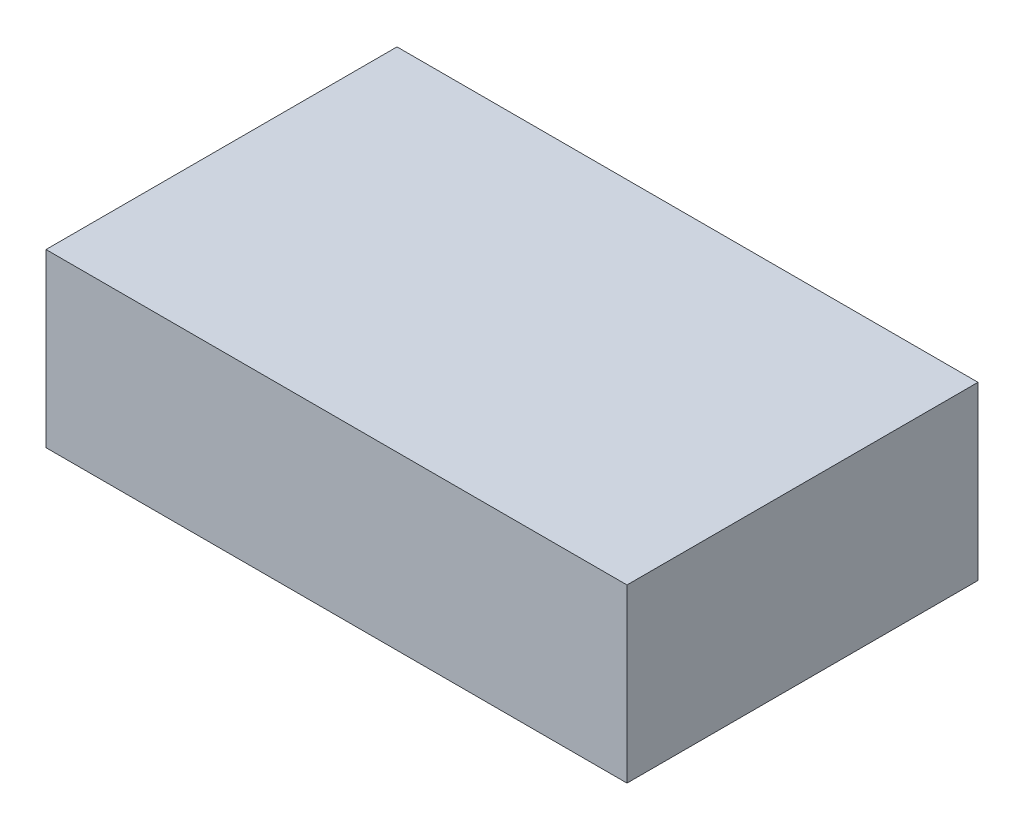
SolidWorks part; units mm, degrees
material "Brass"
ref_plane "Front Plane" through (0, 0, 0) normal (0, 0, 1) x (1, 0, 0)
ref_plane "Top Plane" through (0, 0, 0) normal (0, 1, 0) x (1, 0, 0)
ref_plane "Right Plane" through (0, 0, 0) normal (1, 0, 0) x (0, 0, -1)
sketch "Sketch1" plane through (0, 0, 0) normal (0, 1, 0) x (1, 0, 0)
  line L0 (1.38, -1.38) -> (3.92, -1.38) construction
  line L1 (0, 0) -> (18, 0)
  line L2 (0, 0) -> (0, -13)
  line L3 (0, -13) -> (18, -13)
  line L4 (18, 0) -> (18, -13)
  circle A0 centre (1.38, -1.38) radius 0.5
  circle A1 centre (3.92, -1.38) radius 0.5
  circle A2 centre (6.46, -1.38) radius 0.5
  circle A3 centre (9, -1.38) radius 0.5
  circle A4 centre (11.54, -1.38) radius 0.5
  circle A5 centre (14.08, -1.38) radius 0.5
  circle A6 centre (16.62, -1.38) radius 0.5
  circle A7 centre (2.63, -10.37) radius 1.5
  dimension "D3" = 7
  dimension "D5" = 1
  dimension "D8" = 3
  dimension "D1" = 18
  dimension "D2" = 13
  dimension "D4" = 2.54
  dimension "D6" = 1.38
  dimension "D7" = 1.38
  dimension "D9" = 2.63
  dimension "D10" = 2.63
extrude "Boss-Extrude1" add sketch "Sketch1" against normal blind 1.5
sketch "Sketch2" plane through (0, 0, 0) normal (0, 1, 0) x (1, 0, 0)
  line L1 (6.8313, -8.4994) -> (11.9086, -8.4994)
  line L2 (6.8313, -8.4994) -> (6.8313, -11.5667)
  line L3 (6.8313, -11.5667) -> (11.9086, -11.5667)
  line L4 (0, 0) -> (0, -13)
  line L5 (0, -13) -> (18, -13)
  line L6 (18, -13) -> (18, 0)
  line L7 (18, 0) -> (0, 0)
  line L8 (0, 0) -> (0, -13)
  line L9 (0, -13) -> (18, -13)
  line L10 (18, -13) -> (18, 0)
  line L11 (18, 0) -> (0, 0)
  line L12 (11.9086, -8.4994) -> (11.9086, -11.5667)
  dimension "D1" = 0
extrude "Cut-Extrude1" cut sketch "Sketch2" against normal through all
